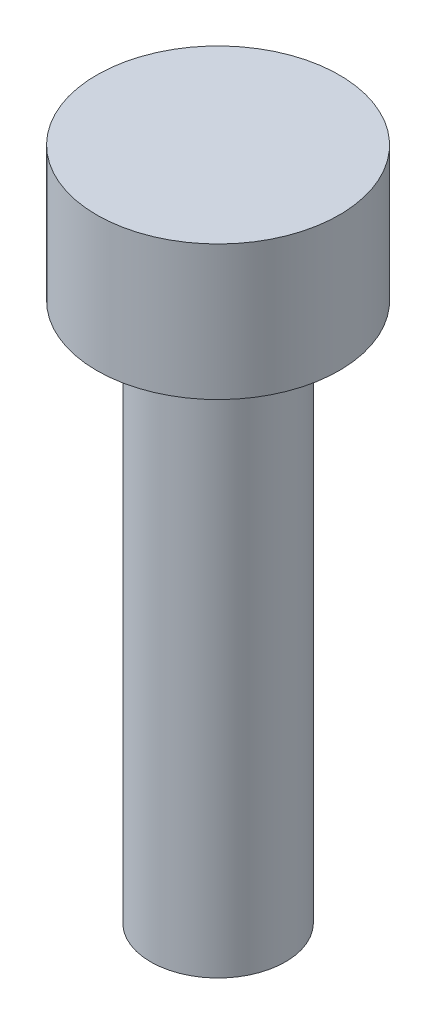
SolidWorks part; units mm, degrees
ref_plane "Front Plane" through (0, 0, 0) normal (0, 0, 1) x (1, 0, 0)
ref_plane "Top Plane" through (0, 0, 0) normal (0, 1, 0) x (1, 0, 0)
ref_plane "Right Plane" through (0, 0, 0) normal (1, 0, 0) x (0, 0, -1)
sketch "Sketch1" plane through (0, 0, 0) normal (0, 1, 0) x (1, 0, 0)
  circle A0 centre (0, 0) radius 1.5
  dimension "D1" = 3
extrude "Boss-Extrude1" add sketch "Sketch1" along normal blind 12
sketch "Sketch2" plane through (0, 12, 0) normal (0, 1, 0) x (1, 0, 0)
  circle A0 centre (0, 0) radius 2.7
  dimension "D1" = 5.4
extrude "Boss-Extrude2" add sketch "Sketch2" along normal blind 3
